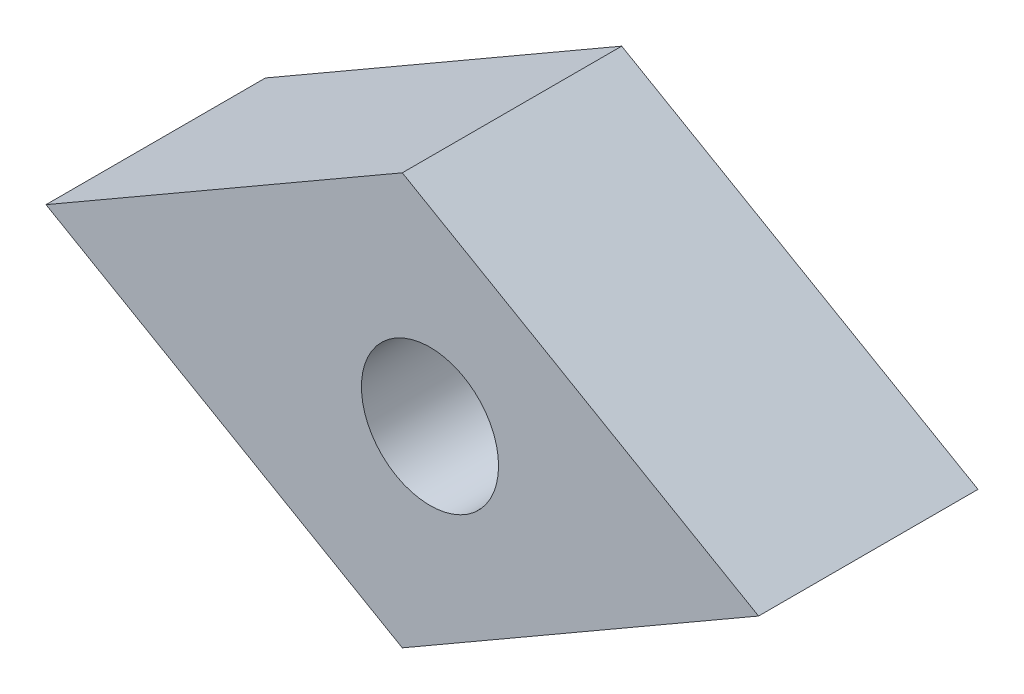
SolidWorks part; units mm, degrees
ref_plane "前视基准面" through (0, 0, 0) normal (0, 0, 1) x (1, 0, 0)
ref_plane "上视基准面" through (0, 0, 0) normal (0, 1, 0) x (1, 0, 0)
ref_plane "右视基准面" through (0, 0, 0) normal (1, 0, 0) x (0, 0, -1)
sketch "草图1" plane through (0, 0, 0) normal (0, 0, 1) x (1, 0, 0)
  line L0 (-41.5931, 0) -> (42.313, 0) construction
  line L1 (0, 50.4905) -> (0, -31.7375) construction
  line L2 (0, 7.5) -> (-12.9904, 0)
  line L3 (-12.9904, 0) -> (0, -7.5)
  line L4 (0, -7.5) -> (12.9904, 0)
  line L5 (12.9904, 0) -> (0, 7.5)
  dimension "D1" = 30
  dimension "D2" = 60
  dimension "D3" = 15
extrude "凸台-拉伸1" add sketch "草图1" along normal blind 8
hole_wizard "孔3" positions "3D草图3" profile "草图6" legacy
sketch3d "3D草图3"
  line L0 (-12.9904, 0, 8) -> (1.0096, 0, 8) construction
  line L2 (0, 7.5, 8) -> (-12.9904, 0, 8) construction
  point P0 (1.0096, 0, 8)
  dimension "D1" = 14
  dimension "D2" = 30
sketch "草图6" plane through (1.0096, 0, 8) normal (1, 0, 0) x (0, -1, 0)
  line L0 (0, 0) -> (0, 9)
  line L1 (0, 9) -> (1.5, 9)
  line L2 (1.5, 9) -> (1.5, 4)
  line L3 (1.5, 4) -> (2.5, 4)
  line L4 (2.5, 4) -> (2.5, 0)
  line L5 (2.5, 0) -> (0, 0)
  line L6 (0, 110) -> (0, -10) construction
  dimension "直径" = 3
  dimension "深度" = 9
  dimension "柱坑直径" = 5
  dimension "柱坑深度" = 4
cosmetic thread "装饰螺纹线1" parameters "D2"=9
